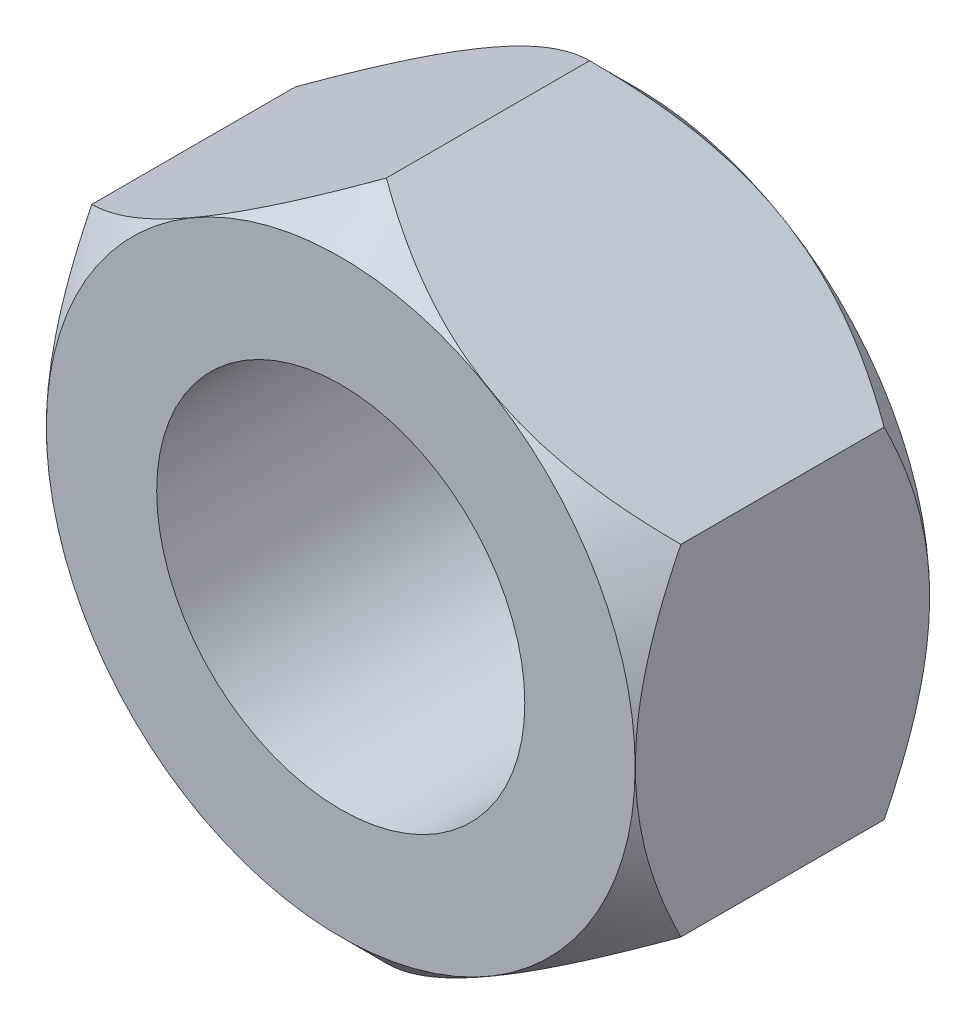
SolidWorks part; units mm, degrees
ref_plane "前视基准面" through (0, 0, 0) normal (0, 0, 1) x (1, 0, 0)
ref_plane "上视基准面" through (0, 0, 0) normal (0, 1, 0) x (1, 0, 0)
ref_plane "右视基准面" through (0, 0, 0) normal (1, 0, 0) x (0, 0, -1)
sketch "草图1" plane through (0, 0, 0) normal (0, 0, 1) x (1, 0, 0)
  line L7 (0, 4.6188) -> (-4, 2.3094)
  line L8 (-4, 2.3094) -> (-4, -2.3094)
  line L9 (-4, -2.3094) -> (0, -4.6188)
  line L10 (0, -4.6188) -> (4, -2.3094)
  line L11 (4, -2.3094) -> (4, 2.3094)
  line L12 (4, 2.3094) -> (0, 4.6188)
  circle A0 centre (0, 0) radius 4 construction
  dimension "D1" = 8
extrude "凸台-拉伸1" add sketch "草图1" along normal blind 4
sketch "草图2" plane through (0, 0, 4) normal (0, 0, 1) x (1, 0, 0)
  circle A0 centre (0, 0) radius 2.5
extrude "切除-拉伸1" cut sketch "草图2" against normal blind 4
fillet "圆角1" radius 0.1 1 edges at (2.5, 0, 0)
sketch "草图3" plane through (0, 0, 0) normal (1, 0, 0) x (0, 0, -1)
  line L0 (0, 0) -> (1.5276, 0) construction
  line L1 (0, -2.3094) -> (0, 2.3094) construction
  line L2 (0, 4.6188) -> (0, 3.9988)
  line L3 (0, 2.3094) -> (0, 4.6188) construction
  line L4 (0, 3.9988) -> (-0.62, 4.6188)
  line L5 (-4, 4.6188) -> (0, 4.6188) construction
  line L6 (-0.62, 4.6188) -> (0, 4.6188)
  line L7 (-3.38, 4.6188) -> (-4, 3.9988)
  line L8 (-4, 2.3094) -> (-4, 4.6188) construction
  line L9 (-4, 3.9988) -> (-4, 4.6188)
  line L10 (-4, 4.6188) -> (-3.38, 4.6188)
revolve "切除-旋转2" cut sketch "草图3" angle 360 about L0
